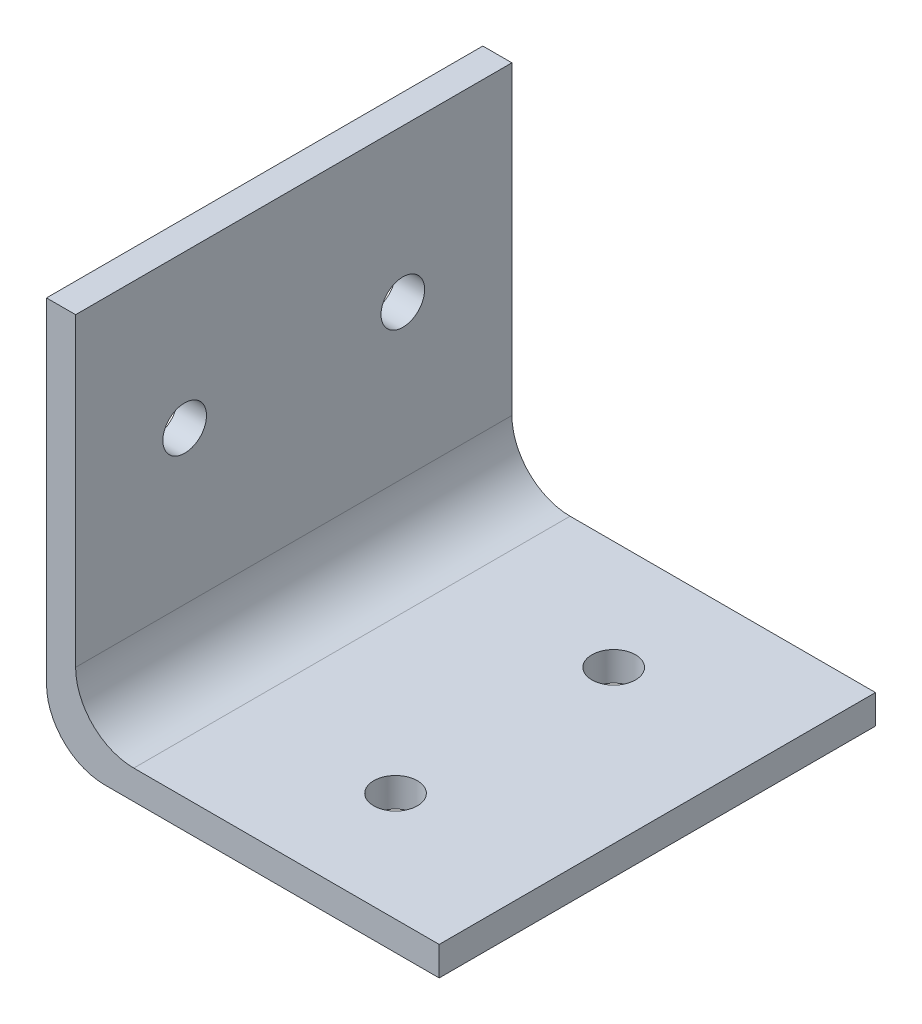
SolidWorks part; units mm, degrees
ref_plane "Front Plane" through (0, 0, 0) normal (0, 0, 1) x (1, 0, 0)
ref_plane "Top Plane" through (0, 0, 0) normal (0, 1, 0) x (1, 0, 0)
ref_plane "Right Plane" through (0, 0, 0) normal (1, 0, 0) x (0, 0, -1)
sketch "Sketch1" plane through (0, 0, 0) normal (0, 0, 1) x (1, 0, 0)
  line L0 (0, 0) -> (25, 0)
  line L1 (25, 0) -> (25, -2)
  line L2 (25, -2) -> (-2, -2)
  line L3 (-2, -2) -> (-2, 25)
  line L4 (-2, 25) -> (0, 25)
  line L5 (0, 25) -> (0, 0)
  dimension "D1" = 25
  dimension "D2" = 25
  dimension "D3" = 2
  dimension "D4" = 2
extrude "Boss-Extrude1" add sketch "Sketch1" against normal blind 30
fillet "Fillet1" radius 4 1 edges at (0, 0, -15)
fillet "Fillet2" radius 4 1 edges at (-2, -2, -15)
sketch "Sketch2" plane through (0, 0, 0) normal (0, 1, 0) x (1, 0, 0)
  line L0 (4, 30) -> (4, 0) construction
  line L1 (-16.9377, 15) -> (66.0072, 15) construction
  point P0 (14.5, 22.5)
  point P2 (14.5, 7.5)
  dimension "D1" = 10.5
  dimension "D2" = 15
  dimension "D3" = 7.5
hole_wizard "Ø3.0mm Dowel Hole1" positions "Sketch3" profile "Sketch4" hole size "Ø3.0" standard "ANSI Metric" end condition up to next
sketch "Sketch3" plane through (0, 0, 0) normal (0, 1, 0) x (1, 0, 0)
  point P0 (14.5, 22.5)
  point P3 (14.5, 7.5)
sketch "Sketch4" plane through (14.5, 0, -22.5) normal (1, 0, 0) x (0, 0, 1)
  line L0 (0, 0) -> (0, 2)
  line L1 (0, 2) -> (1.5, 2)
  line L2 (1.5, 2) -> (1.5, 0)
  line L5 (1.5, 0) -> (0, 0)
  line L11 (0, -6.35) -> (0, 107.95) construction
  dimension "Thru Hole Dia." = 3
  dimension "Thru Hole Depth" = 2
sketch "Sketch5" plane through (0, 0, 0) normal (1, 0, 0) x (0, 0, -1)
  line L0 (-12.1508, 14.5) -> (59.0549, 14.5) construction
  line L1 (0, 4) -> (30, 4) construction
  line L2 (15, 52.8677) -> (15, -15.0924) construction
  line L3 (0, 4) -> (0, 25) construction
  point P8 (7.5, 14.5)
  point P9 (22.5, 14.5)
  dimension "D1" = 10.5
  dimension "D2" = 15
  dimension "D3" = 7.5
hole_wizard "Ø3.0mm Dowel Hole2" positions "Sketch6" profile "Sketch7" hole size "Ø3.0" standard "ANSI Metric" end condition up to next
sketch "Sketch6" plane through (0, 0, 0) normal (1, 0, 0) x (0, 0, -1)
  point P0 (7.5, 14.5)
  point P3 (22.5, 14.5)
sketch "Sketch7" plane through (0, 14.5, -7.5) normal (0, 1, 0) x (0, 0, -1)
  line L0 (0, 0) -> (0, 2)
  line L1 (0, 2) -> (1.5, 2)
  line L2 (1.5, 2) -> (1.5, 0)
  line L5 (1.5, 0) -> (0, 0)
  line L11 (0, -6.35) -> (0, 107.95) construction
  dimension "Thru Hole Dia." = 3
  dimension "Thru Hole Depth" = 2
equation "\"Height\"= 25"
equation "\"D1@Sketch1\"=\"Height\""
equation "\"D2@Sketch1\"=\"Height\""
equation "\"Thick\"=2"
equation "\"D3@Sketch1\"=\"Thick\""
equation "\"D4@Sketch1\"=\"Thick\""
equation "\"Length\"= 30"
equation "\"D1@Boss-Extrude1\"=\"Length\""
equation "\"D1@Sketch2\"=(\"Height\"-4)/2"
equation "\"D2@Sketch2\"=\"Length\"/2"
equation "\"D3@Sketch2\"=\"Length\"/4"
equation "\"D1@Sketch5\"=(\"Height\"-4)/2"
equation "\"D2@Sketch5\"=\"Length\"/2"
equation "\"D3@Sketch5\"=\"Length\"/4"
